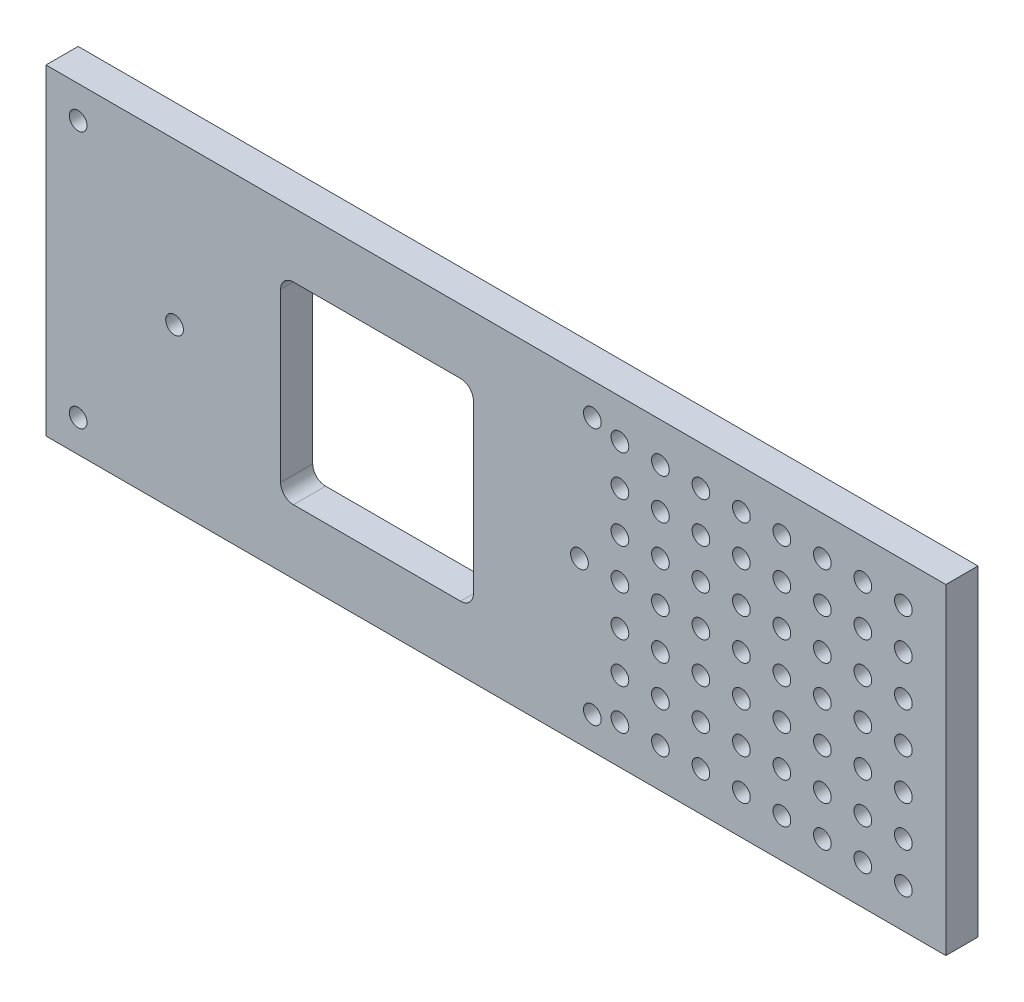
SolidWorks part; units mm, degrees
material "Pine"
ref_plane "Front Plane" through (0, 0, 0) normal (0, 0, 1) x (1, 0, 0)
ref_plane "Top Plane" through (0, 0, 0) normal (0, 1, 0) x (1, 0, 0)
ref_plane "Right Plane" through (0, 0, 0) normal (1, 0, 0) x (0, 0, -1)
sketch "Sketch2" plane through (0, 0, 0) normal (0, 0, 1) x (1, 0, 0)
  line L1 (0, 0) -> (114.3, 0)
  line L2 (0, 0) -> (0, 63.5)
  line L3 (0, 63.5) -> (114.3, 63.5)
  line L4 (114.3, 0) -> (114.3, 63.5)
  dimension "D1" = 114.3
  dimension "D2" = 63.5
extrude "Boss-Extrude1" add sketch "Sketch2" along normal blind 6.35
sketch "Sketch3" plane through (0, 0, 6.35) normal (0, 0, 1) x (1, 0, 0)
  line L0 (25.4, 31.75) -> (105.4, 31.75) construction
  line L11 (25.4, 31.75) -> (6.35, 31.75) construction
  line L12 (0, 63.5) -> (0, 0) construction
  line L15 (107.95, 6.35) -> (107.95, 57.15)
  line L16 (6.35, 6.35) -> (107.95, 6.35)
  line L17 (6.35, 57.15) -> (6.35, 6.35)
  line L18 (107.95, 57.15) -> (6.35, 57.15)
  line L19 (107.95, 6.35) -> (107.95, 57.15) construction
  line L20 (6.35, 6.35) -> (107.95, 6.35) construction
  line L21 (6.35, 57.15) -> (6.35, 6.35) construction
  line L22 (107.95, 57.15) -> (6.35, 57.15) construction
  circle A0 centre (25.4, 31.75) radius 1.75
  circle A1 centre (105.4, 31.75) radius 1.75
  circle A2 centre (6.35, 57.15) radius 1.75
  circle A3 centre (6.35, 6.35) radius 1.75
  circle A4 centre (107.95, 6.35) radius 1.75
  circle A5 centre (107.95, 57.15) radius 1.75
  point P12 (0, 31.75)
  dimension "D2" = 3.5
  dimension "D4" = 3.5
  dimension "D5" = 25.4
  dimension "D1" = 80
  dimension "D3" = 6.35
extrude "Cut-Extrude1" cut sketch "Sketch3" against normal through all
sketch "Sketch4" plane through (0, 0, 6.35) normal (0, 0, 1) x (1, 0, 0)
  line L0 (114.3, 0) -> (177.8, 0)
  line L1 (177.8, 0) -> (177.8, 63.5)
  line L2 (0, 63.5) -> (0, 0) construction
  line L3 (177.8, 63.5) -> (114.3, 63.5)
  line L6 (114.3, 63.5) -> (114.3, 0)
  dimension "D1" = 177.8
extrude "Boss-Extrude2" add sketch "Sketch4" against normal through all contours L3 L6 L0 L1
sketch "Sketch5" plane through (0, 0, 6.35) normal (0, 0, 1) x (1, 0, 0)
  line L1 (105.4, 31.75) -> (113.4, 31.75) construction
  circle A0 centre (113.4, 31.75) radius 1.75
  dimension "D2" = 3.5
  dimension "D1" = 8
extrude "Cut-Extrude2" cut sketch "Sketch5" against normal through all
pattern_linear "LPattern1" count 8 spacing 8 along (1, 0, 0) count 4 spacing 8 along (0, -1, 0) of "Cut-Extrude2"
pattern_linear "LPattern2" count 8 spacing 8 along (1, 0, 0) count 4 spacing 8 along (0, 1, 0) of "Cut-Extrude2"
sketch "Sketch6" plane through (0, 0, 6.35) normal (0, 0, 1) x (1, 0, 0)
  line L0 (25.4, 31.75) -> (105.4, 31.75) construction
  line L2 (84.45, 12.7) -> (46.35, 12.7)
  line L3 (84.45, 12.7) -> (84.45, 50.8)
  line L4 (84.45, 50.8) -> (46.35, 50.8)
  line L5 (46.35, 12.7) -> (46.35, 50.8)
  line L6 (84.45, 12.7) -> (46.35, 50.8) construction
  line L7 (84.45, 50.8) -> (46.35, 12.7) construction
  point P3 (65.4, 31.75)
  dimension "D1" = 38.1
extrude "Cut-Extrude3" cut sketch "Sketch6" against normal through all
fillet "Fillet1" radius 2.54 4 edges at (46.35, 12.7, 3.175) (84.45, 12.7, 3.175) (84.45, 50.8, 3.175) (46.35, 50.8, 3.175)
